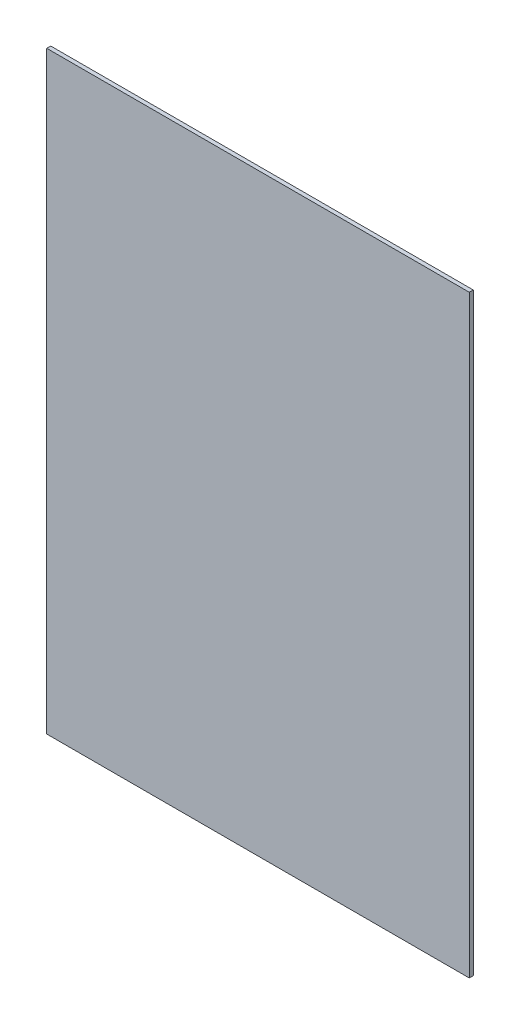
SolidWorks part; units mm, degrees
ref_plane "Front Plane" through (0, 0, 0) normal (0, 0, 1) x (1, 0, 0)
ref_plane "Top Plane" through (0, 0, 0) normal (0, 1, 0) x (1, 0, 0)
ref_plane "Right Plane" through (0, 0, 0) normal (1, 0, 0) x (0, 0, -1)
sketch "Sketch1" plane through (0, 0, 0) normal (0, 0, 1) x (1, 0, 0)
  line L1 (0, 0) -> (539.9532, 0)
  line L2 (0, 0) -> (0, 758.9266)
  line L3 (0, 758.9266) -> (539.9532, 758.9266)
  line L4 (539.9532, 0) -> (539.9532, 758.9266)
  dimension "D1" = 758.9266
  dimension "D2" = 539.9532
extrude "Boss-Extrude1" add sketch "Sketch1" along normal blind 5.08 contours L3 L4 L1 L2
